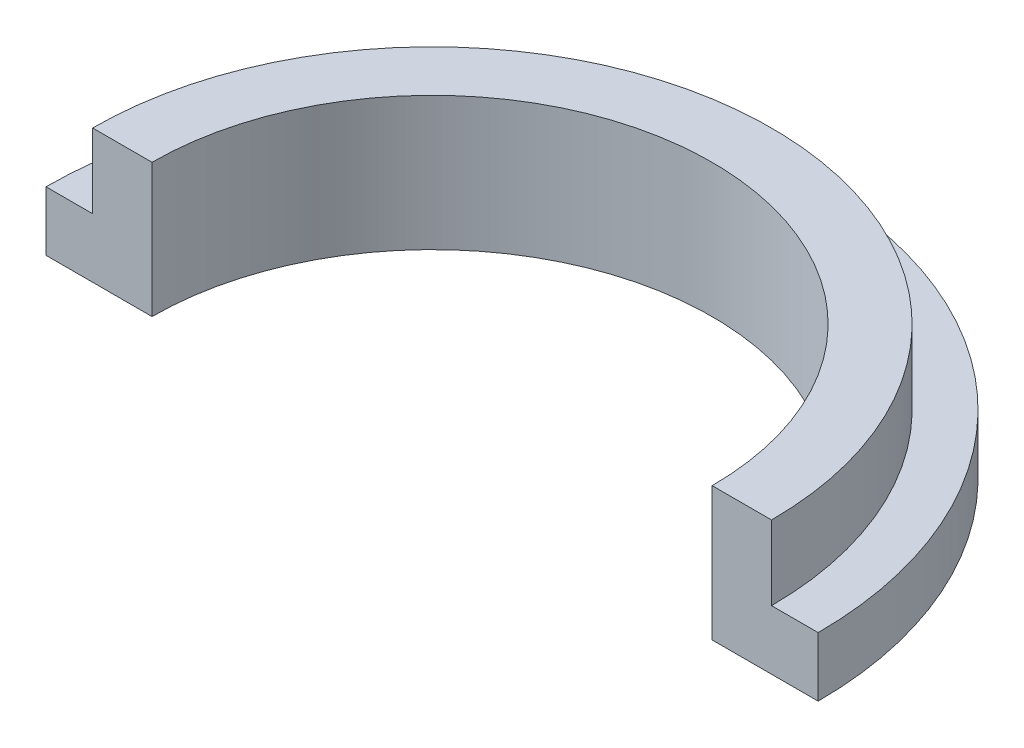
SolidWorks part; units mm, degrees
ref_plane "Front Plane" through (0, 0, 0) normal (0, 0, 1) x (1, 0, 0)
ref_plane "Top Plane" through (0, 0, 0) normal (0, 1, 0) x (1, 0, 0)
ref_plane "Right Plane" through (0, 0, 0) normal (1, 0, 0) x (0, 0, -1)
sketch "Sketch1" plane through (0, 0, 0) normal (0, 1, 0) x (1, 0, 0)
  line L0 (-13, 0) -> (-9.43, 0)
  line L1 (9.43, 0) -> (13, 0)
  circle A0 centre (0, 0) radius 12.43 construction
  circle A1 centre (0, 0) radius 9.43 construction
  circle A2 centre (0, 0) radius 13 construction
  circle A3 centre (0, 0) radius 9.43 construction
  arc A4 (9.43, 0) -> (-9.43, 0) centre (0, 0) ccw
  arc A5 (13, 0) -> (-13, 0) centre (0, 0) ccw
  dimension "D1" = 18.86
  dimension "D2" = 24.86
  dimension "D3" = 26
  dimension "D4" = 18.86
extrude "Boss-Extrude1" add sketch "Sketch1" along normal blind 4.5
sketch "Sketch2" plane through (0, 4.5, 0) normal (0, 1, 0) x (1, 0, 0)
  line L2 (-13, 0) -> (-11.43, 0)
  line L3 (11.43, 0) -> (13, 0)
  arc A1 (13, 0) -> (-13, 0) centre (0, 0) ccw construction
  arc A2 (11.43, 0) -> (-11.43, 0) centre (0, 0) ccw
  arc A3 (11.43, 0) -> (-11.43, 0) centre (0, 0) ccw
  arc A4 (13, 0) -> (-13, 0) centre (0, 0) ccw
  dimension "D1" = 2
extrude "Cut-Extrude1" cut sketch "Sketch2" against normal blind 2.5
